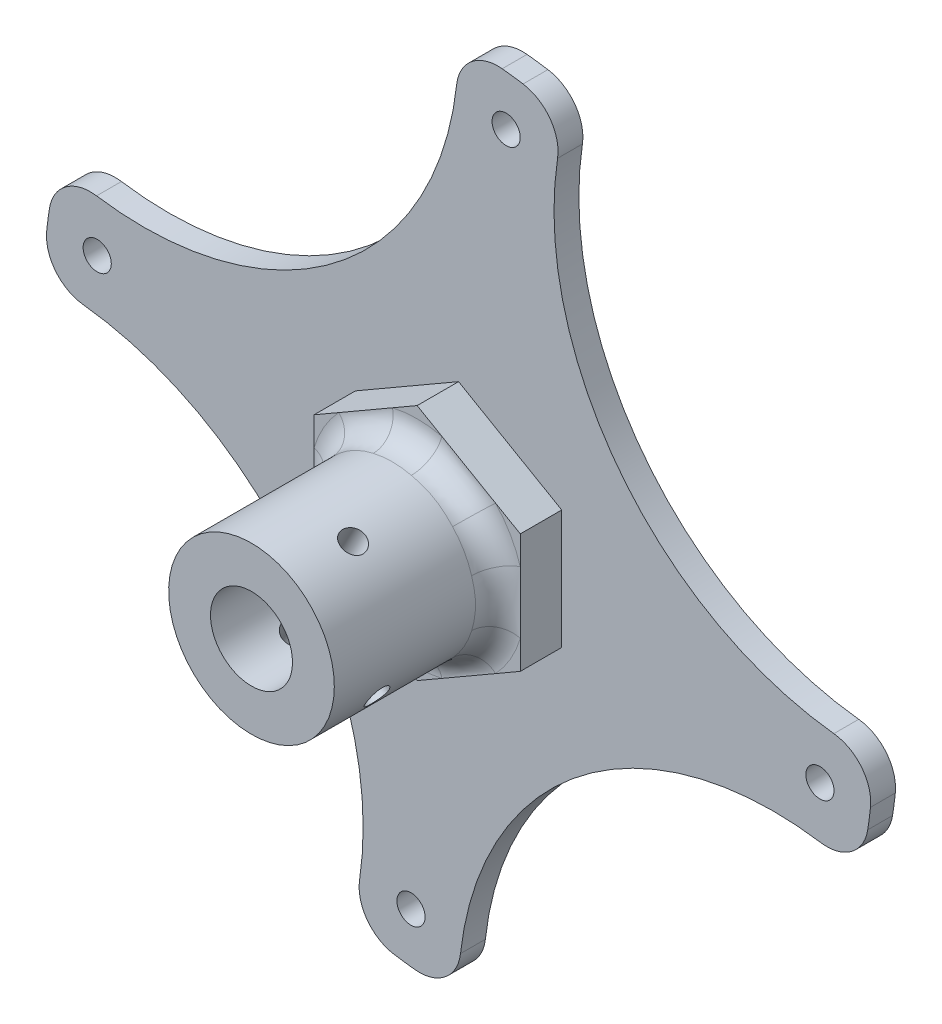
SolidWorks part; units mm, degrees
ref_plane "Front Plane" through (0, 0, 0) normal (0, 0, 1) x (1, 0, 0)
ref_plane "Top Plane" through (0, 0, 0) normal (0, 1, 0) x (1, 0, 0)
ref_plane "Right Plane" through (0, 0, 0) normal (1, 0, 0) x (0, 0, -1)
sketch "Sketch1" plane through (0, 0, 0) normal (0, 0, 1) x (1, 0, 0)
  circle A0 centre (0, 0) radius 50
  dimension "D1" = 100
extrude "Boss-Extrude1" add sketch "Sketch1" along normal blind 3
sketch "Sketch2" plane through (0, 0, 3) normal (0, 0, 1) x (1, 0, 0)
  line L1 (12.45, -7.188) -> (12.45, 7.188)
  line L2 (12.45, 7.188) -> (0, 14.376)
  line L3 (0, 14.376) -> (-12.45, 7.188)
  line L4 (-12.45, 7.188) -> (-12.45, -7.188)
  line L5 (-12.45, -7.188) -> (0, -14.376)
  line L6 (0, -14.376) -> (12.45, -7.188)
  circle A0 centre (0, 0) radius 12.45 construction
  dimension "D1" = 24.9
extrude "Boss-Extrude2" add sketch "Sketch2" along normal blind 5
sketch "Sketch3" plane through (0, 0, 8) normal (0, 0, 1) x (1, 0, 0)
  circle A0 centre (0, 0) radius 10
  dimension "D1" = 20
extrude "Boss-Extrude3" add sketch "Sketch3" along normal blind 20
fillet "Fillet1" radius 3 1 edges at (10, 0, 8)
sketch "Sketch4" plane through (0, 0, 28) normal (0, 0, 1) x (1, 0, 0)
  circle A0 centre (0, 0) radius 4.95
  dimension "D1" = 9.9
extrude "Cut-Extrude1" cut sketch "Sketch4" against normal through all
hole_wizard "Ø1.0mm Dowel Hole1" positions "3DSketch1" profile "Sketch5" hole size "Ø1.0" standard "ANSI Metric"
sketch3d "3DSketch1"
  point P0 (-8.6665, 4.9891, 21.4992)
  point P2 (4.7386, 8.806, 20.4576)
sketch "Sketch5" plane through (-8.6665, 4.9891, 21.4992) normal (0, 0, 1) x (-0.4989, -0.8667, 0)
  line L0 (0, 0) -> (0, 34)
  line L1 (0, 34) -> (1.4, 33.1588)
  line L2 (1.4, 33.1588) -> (1.4, 0)
  line L5 (1.4, 0) -> (0, 0)
  line L10 (0, 34) -> (-1.4, 33.1588) construction
  line L11 (0, -6.35) -> (0, 107.95) construction
  dimension "Hole Dia." = 2.8
  dimension "Hole Depth" = 34
  dimension "Drill Angle" = 118
sketch "Sketch6" plane through (0, 0, 3) normal (0, 0, 1) x (1, 0, 0)
  line L0 (-50, 0) -> (0, 0)
  line L1 (0, 0) -> (-48.2963, 12.941)
  arc A0 (0, 50) -> (-48.2963, 12.941) centre (-37.997, 49.5186) cw
  circle A1 centre (0, 0) radius 50 construction
  arc A2 (-48.2963, 12.941) -> (0, 50) centre (0, 0) ccw
  arc A3 (50, 0) -> (12.941, 48.2963) centre (49.5186, 37.997) cw
  arc A4 (0, -50) -> (48.2963, -12.941) centre (37.997, -49.5186) cw
  arc A5 (-50, 0) -> (-12.941, -48.2963) centre (-49.5186, -37.997) cw
  point P21 (0, 0)
  circle M9 centre (0, 0) radius 50
  dimension "D1" = 38
  dimension "D3" = 4
  dimension "15" = 15
extrude "Cut-Extrude2" cut sketch "Sketch6" against normal blind 25 contours A0 L1 M9 | A3 A2 | A4 A2 | A5 L0 M9
fillet "Fillet2" radius 5 8 edges at (-48.2963, 12.941, 1.5) (-50, 0, 1.5) (-12.941, -48.2963, 1.5) (48.2963, -12.941, 1.5) (0, -50, 1.5) (12.941, 48.2963, 1.5) (50, 0, 1.5) (0, 50, 1.5)
sketch "Sketch7" plane through (0, 0, 0) normal (0, 0, -1) x (-1, 0, 0)
  line L0 (-6.5263, 49.5722) -> (0, 0) construction
  arc A0 (-5.2642, 49.7221) -> (-7.7842, 49.3903) centre (0, 0) ccw construction
  point P0 (-5.7432, 43.6236)
  point P10 (43.6236, 5.7432)
  point P11 (5.7432, -43.6236)
  point P12 (-43.6236, -5.7432)
  point P13 (0, 0)
  dimension "D1" = 6
  dimension "D2" = 4
hole_wizard "Ø1.0mm Dowel Hole2" positions "3DSketch2" profile "Sketch8" hole size "Ø1.0" standard "ANSI Metric"
sketch3d "3DSketch2"
  point P0 (5.7432, 43.6236, 0)
  point P3 (-43.6236, 5.7432, 0)
  point P6 (-5.7432, -43.6236, 0)
  point P9 (43.6236, -5.7432, 0)
sketch "Sketch8" plane through (5.7432, 43.6236, 0) normal (1, 0, 0) x (0, 1, 0)
  line L0 (0, 0) -> (0, 34)
  line L1 (0, 34) -> (1.7, 32.9785)
  line L2 (1.7, 32.9785) -> (1.7, 0)
  line L5 (1.7, 0) -> (0, 0)
  line L10 (0, 34) -> (-1.7, 32.9785) construction
  line L11 (0, -6.35) -> (0, 107.95) construction
  dimension "Hole Dia." = 3.4
  dimension "Hole Depth" = 34
  dimension "Drill Angle" = 118
